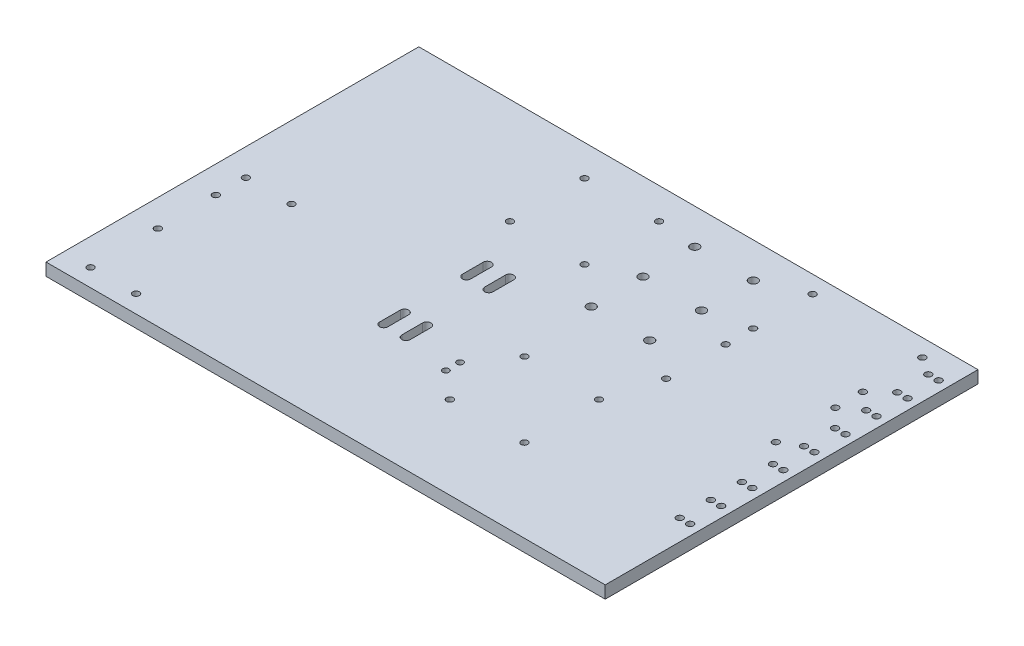
SolidWorks part; units mm, degrees
material "Balsa"
ref_plane "Front Plane" through (0, 0, 0) normal (0, 0, 1) x (1, 0, 0)
ref_plane "Top Plane" through (0, 0, 0) normal (0, 1, 0) x (1, 0, 0)
ref_plane "Right Plane" through (0, 0, 0) normal (1, 0, 0) x (0, 0, -1)
sketch "Sketch1" plane through (0, 0, 0) normal (0, 1, 0) x (1, 0, 0)
  line L1 (135, -90) -> (-135, -90)
  line L2 (135, -90) -> (135, 90)
  line L3 (135, 90) -> (-135, 90)
  line L4 (-135, -90) -> (-135, 90)
  line L5 (135, -90) -> (-135, 90) construction
  line L6 (135, 90) -> (-135, -90) construction
  point P0 (0, 0)
  dimension "D1" = 180
  dimension "D2" = 270
extrude "Boss-Extrude1" add sketch "Sketch1" along normal blind 6
sketch "Sketch2" plane through (0, 0, 0) normal (0, -1, 0) x (1, 0, 0)
  line L0 (-128.328, 81.5) -> (-96.2467, 81.5) construction
  line L1 (-122, 85.0517) -> (-122, -13.5) construction
  circle A1 centre (-122, 81.5) radius 1.6
  circle A2 centre (-100, 81.5) radius 1.6
  circle A4 centre (-122, 6.5) radius 1.6
  circle A5 centre (-100, 6.5) radius 1.6
  circle A7 centre (-122, 21) radius 1.6
  circle A8 centre (-122, 49) radius 1.6
  dimension "D1" = 3.2
  dimension "D2" = 3.2
  dimension "D3" = 3.2
  dimension "D4" = 3.2
  dimension "D5" = 3.2
  dimension "D6" = 3.2
extrude "Cut-Extrude1" cut sketch "Sketch2" against normal through all
sketch "Sketch3" plane through (0, 0, 0) normal (0, -1, 0) x (1, 0, 0)
  line L0 (-40, -39) -> (-4, -39) construction
  line L1 (-4, -39) -> (-4, -75) construction
  line L2 (-4, -75) -> (-40, -75) construction
  line L3 (-40, -75) -> (-40, -39) construction
  line L4 (135, -90) -> (-135, -90) construction
  line L5 (-135, -90) -> (-135, 90) construction
  line L6 (-27.38, -39) -> (-27.38, 69.9889) construction
  line L7 (-16.63, -39) -> (-16.63, 69.9889) construction
  line L8 (-27.38, -15.4585) -> (-27.38, -5.4585) construction
  line L9 (-29.38, -15.4585) -> (-29.38, -5.4585)
  line L10 (-25.38, -15.4585) -> (-25.38, -5.4585)
  line L11 (-27.38, -29.7467) -> (-16.63, -29.7467) construction
  line L13 (-16.63, -15.4585) -> (-16.63, -5.4585) construction
  line L14 (-14.63, -15.4585) -> (-14.63, -5.4585)
  line L15 (-18.63, -15.4585) -> (-18.63, -5.4585)
  line L16 (-22.1289, -38.8574) -> (-22.1289, 8.5719) construction
  line L17 (-27.38, 24.5415) -> (-27.38, 34.5415) construction
  line L18 (-29.38, 24.5415) -> (-29.38, 34.5415)
  line L19 (-25.38, 24.5415) -> (-25.38, 34.5415)
  line L20 (-16.63, 24.5415) -> (-16.63, 34.5415) construction
  line L21 (-14.63, 24.5415) -> (-14.63, 34.5415)
  line L22 (-18.63, 24.5415) -> (-18.63, 34.5415)
  circle A1 centre (-40, -39) radius 1.6
  circle A2 centre (-40, -75) radius 1.6
  circle A3 centre (-4, -75) radius 1.6
  circle A4 centre (-4, -39) radius 1.6
  arc A5 (-29.38, -15.4585) -> (-25.38, -15.4585) centre (-27.38, -15.4585) ccw
  arc A6 (-25.38, -5.4585) -> (-29.38, -5.4585) centre (-27.38, -5.4585) ccw
  arc A7 (-14.63, -15.4585) -> (-18.63, -15.4585) centre (-16.63, -15.4585) cw
  arc A8 (-18.63, -5.4585) -> (-14.63, -5.4585) centre (-16.63, -5.4585) cw
  arc A9 (-29.38, 24.5415) -> (-25.38, 24.5415) centre (-27.38, 24.5415) ccw
  arc A10 (-25.38, 34.5415) -> (-29.38, 34.5415) centre (-27.38, 34.5415) ccw
  arc A11 (-14.63, 24.5415) -> (-18.63, 24.5415) centre (-16.63, 24.5415) cw
  arc A12 (-18.63, 34.5415) -> (-14.63, 34.5415) centre (-16.63, 34.5415) cw
  point P20 (-27.38, -10.4585)
  point P27 (0, 0)
  point P31 (-16.63, -10.4585)
  point P40 (-27.38, 29.5415)
  point P47 (-16.63, 29.5415)
  dimension "D1" = 3.2
  dimension "D2" = 3.2
  dimension "D3" = 3.2
  dimension "D4" = 3.2
  dimension "D10" = 2
  dimension "D5" = 15
  dimension "D6" = 36
  dimension "D7" = 36
  dimension "D8" = 95
  dimension "D9" = 10
  dimension "D11" = 40
extrude "Cut-Extrude2" cut sketch "Sketch3" against normal blind 10
sketch "Sketch4" plane through (0, 6, 0) normal (0, 1, 0) x (1, 0, 0)
  line L0 (20, -14) -> (20, -50) construction
  line L1 (20, -50) -> (55.9999, -50) construction
  line L2 (55.9999, -50) -> (55.9999, -14.0001) construction
  line L3 (55.9999, -14.0001) -> (20, -14) construction
  line L4 (-135, 90) -> (-135, -90) construction
  line L5 (-135, -90) -> (135, -90) construction
  line L6 (17.4999, -32.0001) -> (-2.3281, -32.0001) construction
  line L8 (17.495, -38.8173) -> (-2.3281, -38.8173) construction
  circle A1 centre (20, -14) radius 1.6
  circle A2 centre (55.9999, -14.0001) radius 1.6
  circle A3 centre (20, -50) radius 1.6
  circle A4 centre (55.9999, -50) radius 1.6
  circle A5 centre (6.905, -32.0001) radius 1.5
  circle A6 centre (6.905, -38.8173) radius 1.5
  dimension "D1" = 3.2
  dimension "D2" = 3.2
  dimension "D3" = 3.2
  dimension "D4" = 3.2
  dimension "D9" = 3
  dimension "D10" = 3
  dimension "D5" = 36
  dimension "D6" = 36
  dimension "D7" = 155
  dimension "D8" = 40
extrude "Cut-Extrude3" cut sketch "Sketch4" against normal through all
sketch "Sketch5" plane through (0, 6, 0) normal (0, 1, 0) x (1, 0, 0)
  line L0 (60, 25.2707) -> (120, 25.2707) construction
  line L1 (60, 43.7707) -> (120, 43.7707) construction
  line L2 (60, 43.7707) -> (60, 6.7707) construction
  line L3 (60, 6.7707) -> (120, 6.7707) construction
  line L4 (120, 43.7707) -> (120, 6.7707) construction
  line L5 (90, 43.7707) -> (90, 6.7707) construction
  line L6 (135, -90) -> (135, 90) construction
  line L7 (60, 67.2707) -> (120, 67.2707) construction
  line L8 (60, 85.7707) -> (120, 85.7707) construction
  line L9 (60, 85.7707) -> (60, 48.7707) construction
  line L10 (60, 48.7707) -> (120, 48.7707) construction
  line L11 (120, 85.7707) -> (120, 48.7707) construction
  line L12 (90, 85.7707) -> (90, 48.7707) construction
  line L13 (90, 43.7707) -> (90, 48.7707) construction
  line L14 (125, 76.0006) -> (130, 76.0006) construction
  line L15 (120, 85.7707) -> (135, 85.7707) construction
  line L16 (127.5, 85.7707) -> (127.5, -20.9964) construction
  line L17 (125, 61.0006) -> (130, 61.0006) construction
  line L18 (125, 46.0006) -> (130, 46.0006) construction
  line L19 (125, 31.0006) -> (130, 31.0006) construction
  line L20 (125, 16.0006) -> (130, 16.0006) construction
  line L21 (125, 1.0006) -> (130, 1.0006) construction
  line L22 (125, -13.9994) -> (130, -13.9994) construction
  line L23 (125, -28.9994) -> (130, -28.9994) construction
  line L24 (125, -43.9994) -> (130, -43.9994) construction
  circle A1 centre (116.5, 10.9115) radius 1.6
  circle A2 centre (63.5, 10.9115) radius 1.6
  circle A3 centre (116.5, 39.6298) radius 1.6
  circle A4 centre (63.5, 39.6298) radius 1.6
  circle A9 centre (116.5, 52.9115) radius 1.6
  circle A10 centre (63.5, 52.9115) radius 1.6
  circle A11 centre (116.5, 81.6298) radius 1.6
  circle A12 centre (63.5, 81.6298) radius 1.6
  circle A13 centre (125, 76.0006) radius 1.6
  circle A14 centre (130, 76.0006) radius 1.6
  circle A15 centre (125, 61.0006) radius 1.6
  circle A16 centre (130, 61.0006) radius 1.6
  circle A17 centre (125, 46.0006) radius 1.6
  circle A18 centre (130, 46.0006) radius 1.6
  circle A19 centre (125, 31.0006) radius 1.6
  circle A20 centre (130, 31.0006) radius 1.6
  circle A21 centre (125, 16.0006) radius 1.6
  circle A22 centre (130, 16.0006) radius 1.6
  circle A23 centre (125, 1.0006) radius 1.6
  circle A24 centre (130, 1.0006) radius 1.6
  circle A25 centre (125, -13.9994) radius 1.6
  circle A26 centre (130, -13.9994) radius 1.6
  circle A27 centre (125, -28.9994) radius 1.6
  circle A28 centre (130, -28.9994) radius 1.6
  circle A29 centre (125, -43.9994) radius 1.6
  circle A30 centre (130, -43.9994) radius 1.6
  point P6 (77.5136, 25.2707)
  point P25 (74.5136, 67.2707)
  dimension "D3" = 3.2
  dimension "D1" = 60
  dimension "D2" = 37
  dimension "D4" = 3.5
  dimension "D5" = 15
  dimension "D6" = 5
  dimension "D7" = 5
  dimension "D8" = 9
extrude "Cut-Extrude4" cut sketch "Sketch5" against normal blind 10
sketch "Sketch6" plane through (0, 6, 0) normal (0, 1, 0) x (1, 0, 0)
  line L0 (15.26, 73) -> (43.5, 73) construction
  line L1 (135, 90) -> (-135, 90) construction
  line L2 (63.5, 90) -> (63.5, 9.3115) construction
  line L3 (15.26, 48) -> (43.5, 48) construction
  line L4 (15.26, 23) -> (43.5, 23) construction
  circle A0 centre (15.26, 73) radius 2.1
  circle A1 centre (43.5, 73) radius 2.1
  circle A2 centre (63.5, 10.9115) radius 1.6 construction
  circle A3 centre (15.26, 48) radius 2.1
  circle A4 centre (43.5, 48) radius 2.1
  circle A5 centre (15.26, 23) radius 2.1
  circle A6 centre (43.5, 23) radius 2.1
  dimension "D2" = 4.2
  dimension "D3" = 4.2
  dimension "D1" = 28.24
  dimension "D4" = 17
  dimension "D5" = 20
  dimension "D6" = 3
extrude "Cut-Extrude5" cut sketch "Sketch6" against normal blind 10
